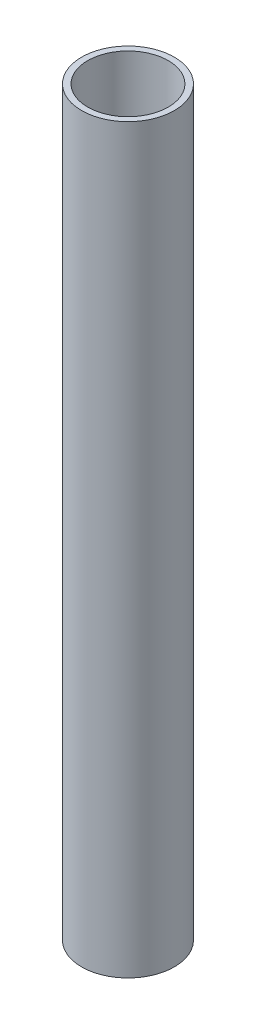
SolidWorks part; units mm, degrees
material "6061-T6 (SS)"
ref_plane "Front Plane" through (0, 0, 0) normal (0, 0, 1) x (1, 0, 0)
ref_plane "Top Plane" through (0, 0, 0) normal (0, 1, 0) x (1, 0, 0)
ref_plane "Right Plane" through (0, 0, 0) normal (1, 0, 0) x (0, 0, -1)
sketch "Sketch1" plane through (0, 0, 0) normal (0, 1, 0) x (1, 0, 0)
  circle A0 centre (0, 0) radius 9.525
  circle A1 centre (0, 0) radius 8.2804
  dimension "D1" = 16.5608
  dimension "D2" = 19.05
extrude "Boss-Extrude1" add sketch "Sketch1" along normal blind 152.4
